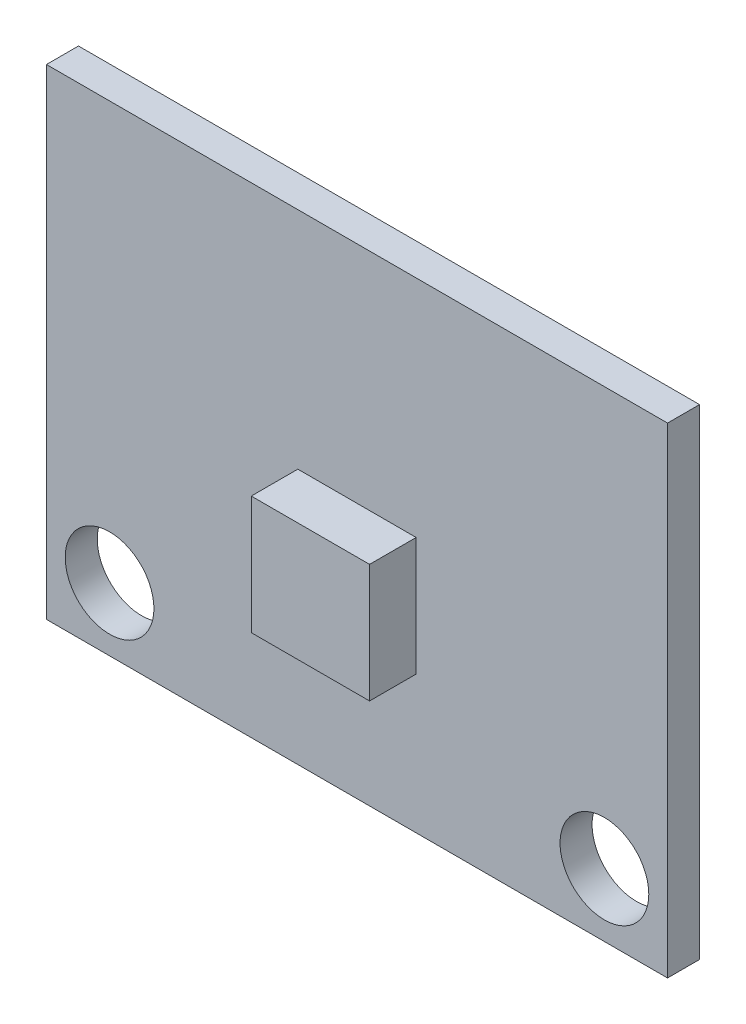
SolidWorks part; units mm, degrees
ref_plane "Front Plane" through (0, 0, 0) normal (0, 0, 1) x (1, 0, 0)
ref_plane "Top Plane" through (0, 0, 0) normal (0, 1, 0) x (1, 0, 0)
ref_plane "Right Plane" through (0, 0, 0) normal (1, 0, 0) x (0, 0, -1)
sketch "Sketch1" plane through (0, 0, 0) normal (0, 0, 1) x (1, 0, 0)
  line L0 (2.168, 2.168) -> (19.168, 2.168) construction
  line L1 (0, 0) -> (21.336, 0)
  line L2 (0, 0) -> (0, 16.51)
  line L3 (0, 16.51) -> (21.336, 16.51)
  line L4 (21.336, 0) -> (21.336, 16.51)
  line L5 (21.336, 2.168) -> (19.168, 2.168) construction
  line L6 (19.168, 2.168) -> (19.168, 0) construction
  circle A0 centre (2.168, 2.168) radius 1.524
  circle A1 centre (19.168, 2.168) radius 1.524
  point P9 (10.668, 0)
  point P10 (10.668, 2.168)
  dimension "D3" = 3.048
  dimension "D1" = 21.336
  dimension "D2" = 16.51
  dimension "D4" = 17
extrude "Boss-Extrude1" add sketch "Sketch1" along normal blind 2.7
sketch "Sketch2" plane through (0, 0, 2.7) normal (0, 0, 1) x (1, 0, 0)
  line L0 (0, 0) -> (21.336, 0) construction
  line L1 (8.636, 8.7884) -> (12.7, 8.7884)
  line L2 (8.636, 8.7884) -> (8.636, 4.7244)
  line L3 (8.636, 4.7244) -> (12.7, 4.7244)
  line L4 (12.7, 8.7884) -> (12.7, 4.7244)
  line L5 (10.668, 8.7884) -> (10.668, 16.51) construction
  line L6 (21.336, 16.51) -> (0, 16.51) construction
  dimension "D1" = 4.064
  dimension "D2" = 4.064
  dimension "D3" = 4.7244
extrude "Cut-Extrude1" cut sketch "Sketch2" against normal blind 1.6002 flip side to cut
